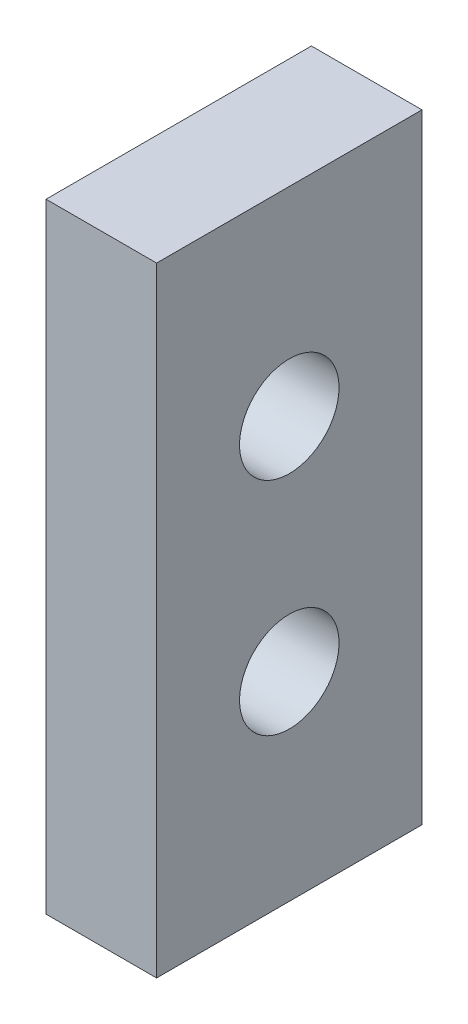
SolidWorks part; units mm, degrees
ref_plane "Front Plane" through (0, 0, 0) normal (0, 0, 1) x (1, 0, 0)
ref_plane "Top Plane" through (0, 0, 0) normal (0, 1, 0) x (1, 0, 0)
ref_plane "Right Plane" through (0, 0, 0) normal (1, 0, 0) x (0, 0, -1)
sketch "Sketch1" plane through (0, 0, 0) normal (1, 0, 0) x (0, 0, -1)
  line L0 (55, 0) -> (-55, 0) construction
  line L1 (6, -14) -> (-6, -14)
  line L2 (6, -14) -> (6, 14)
  line L3 (6, 14) -> (-6, 14)
  line L4 (-6, -14) -> (-6, 14)
  line L5 (6, -14) -> (-6, 14) construction
  line L6 (6, 14) -> (-6, -14) construction
  circle A0 centre (0, 5) radius 2.25
  circle A1 centre (0, -5) radius 2.25
  point P0 (0, 0)
  dimension "D3" = 5
  dimension "D1" = 28
  dimension "D2" = 12
extrude "Boss-Extrude1" add sketch "Sketch1" along normal blind 5
